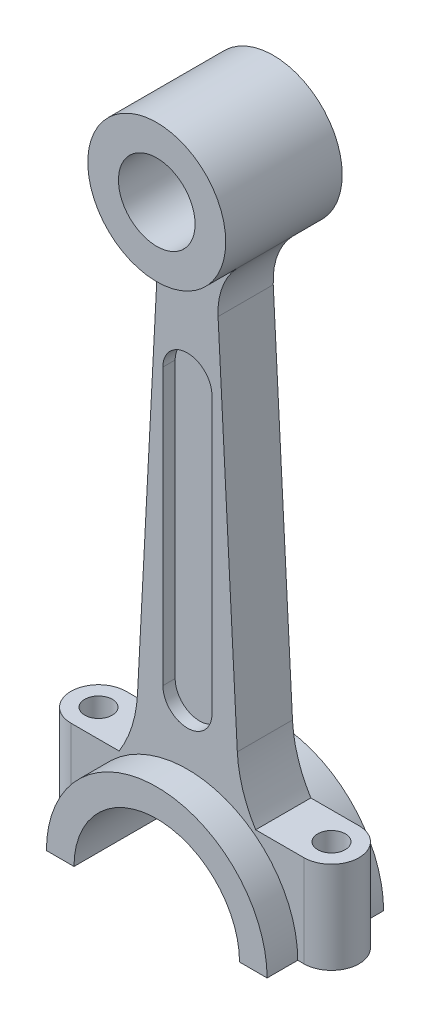
SolidWorks part; units mm, degrees
material "High-leaded brass, UNS C34200"
ref_plane "Front Plane" through (0, 0, 0) normal (0, 0, 1) x (1, 0, 0)
ref_plane "Top Plane" through (0, 0, 0) normal (0, 1, 0) x (1, 0, 0)
ref_plane "Right Plane" through (0, 0, 0) normal (1, 0, 0) x (0, 0, -1)
sketch "Sketch1" plane through (0, 0, 0) normal (0, 0, 1) x (1, 0, 0)
  line L0 (0, -1000) -> (0, 49000) construction
  line L1 (-36, -201.2) -> (36, -201.2)
  circle A0 centre (0, 0) radius 22.5
  arc A1 (36, -201.2) -> (-36, -201.2) centre (0, -201.2) ccw
  dimension "D1" = 201.2
  dimension "D2" = 45
  dimension "D3" = 72
extrude "Boss-Extrude1" add sketch "Sketch1" along normal mid plane 38
sketch "Sketch2" plane through (0, 0, 0) normal (0, 0, 1) x (1, 0, 0)
  line L0 (0, 22.5) -> (0, 49000) construction
  line L1 (-16.2797, -152.1587) -> (-10, -32.3345)
  line L2 (16.2797, -152.1587) -> (10, -32.3345)
  arc A0 (-16.2346, -15.5785) -> (-10, -32.3345) centre (-32.4692, -31.1569) cw
  circle A1 centre (0, 0) radius 22.5 construction
  arc A2 (-26.6328, -176.9783) -> (-16.2797, -152.1587) centre (-56.2249, -150.0653) ccw
  circle A3 centre (0, -201.2) radius 36 construction
  arc A4 (26.6328, -176.9783) -> (16.2797, -152.1587) centre (56.2249, -150.0653) cw
  arc A5 (16.2346, -15.5785) -> (10, -32.3345) centre (32.4692, -31.1569) ccw
  arc A6 (26.6328, -176.9783) -> (-26.6328, -176.9783) centre (0, -201.2) ccw
  arc A7 (-16.2346, -15.5785) -> (16.2346, -15.5785) centre (0, 0) ccw
  dimension "D1" = 22.5
  dimension "D2" = 40
  dimension "D3" = 20
  dimension "D4" = 6
extrude "Boss-Extrude2" add sketch "Sketch2" along normal mid plane 18
sketch "Sketch3" plane through (0, 0, 9) normal (0, 0, 1) x (1, 0, 0)
  line L0 (0, -145.6) -> (0, -55.6) construction
  line L1 (-8, -145.6) -> (-8, -55.6)
  line L2 (8, -145.6) -> (8, -55.6)
  arc A0 (-8, -145.6) -> (8, -145.6) centre (0, -145.6) ccw
  arc A1 (8, -55.6) -> (-8, -55.6) centre (0, -55.6) ccw
  point P3 (0, -100.6)
  dimension "D3" = 8
  dimension "D1" = 90
  dimension "D2" = 100.6
extrude "Cut-Extrude1" cut sketch "Sketch3" against normal blind 4
mirror "Mirror1" about plane through (0, 0, 0) normal (0, 0, 1) of "Cut-Extrude1"
sketch "Sketch5" plane through (0, -201.2, 0) normal (0, -1, 0) x (1, 0, 0)
  line L0 (-1000, 0) -> (49000, 0) construction
  line L1 (0, -1000) -> (0, 49000) construction
  circle A0 centre (-38, 0) radius 4.5
  circle A1 centre (38, 0) radius 4.5
  dimension "D2" = 9
  dimension "D1" = 76
sketch "Sketch6" plane through (0, 0, 0) normal (0, 0, 1) x (1, 0, 0)
  line L0 (0, -1000) -> (0, 49000) construction
  line L1 (47, -201.2) -> (-47, -201.2)
  line L2 (-201000, -201.2) -> (249000, -201.2) construction
  line L3 (-47, -201.2) -> (-47, -171.2)
  line L4 (-47, -171.2) -> (47, -171.2)
  line L5 (47, -171.2) -> (47, -201.2)
  dimension "D1" = 47
  dimension "D2" = 30
extrude "Boss-Extrude3" add sketch "Sketch6" along normal mid plane 18
sketch "Sketch4" plane through (0, 0, 19) normal (0, 0, 1) x (1, 0, 0)
  line L0 (-36, -201.2) -> (36, -201.2) construction
  line L1 (-27, -201.2) -> (27, -201.2)
  circle A0 centre (0, 0) radius 12.5
  arc A1 (27, -201.2) -> (-27, -201.2) centre (0, -201.2) ccw
  dimension "D1" = 25
  dimension "D2" = 27
extrude "Cut-Extrude2" cut sketch "Sketch4" against normal through all
extrude "Cut-Extrude3" cut sketch "Sketch5" against normal through all
sketch "Sketch7" plane through (0, -201.2, 0) normal (0, -1, 0) x (1, 0, 0)
  line L0 (-47, 9) -> (-47, -9)
  line L1 (-47, -9) -> (-38, -9)
  line L2 (-47, 9) -> (-38, 9)
  arc A0 (-38, 9) -> (-38, -9) centre (-38, 0) ccw
  line M6 (-36, 9) -> (-47, 9)
  line M7 (-47, 9) -> (-47, -9)
  line M8 (-47, -9) -> (-36, -9)
  dimension "D1" = 18
extrude "Cut-Extrude4" cut sketch "Sketch7" against normal through all contours A0 L0 M8 | A0 M6 M7
mirror "Mirror2" about plane through (0, 0, 0) normal (1, 0, 0) of "Cut-Extrude4"
